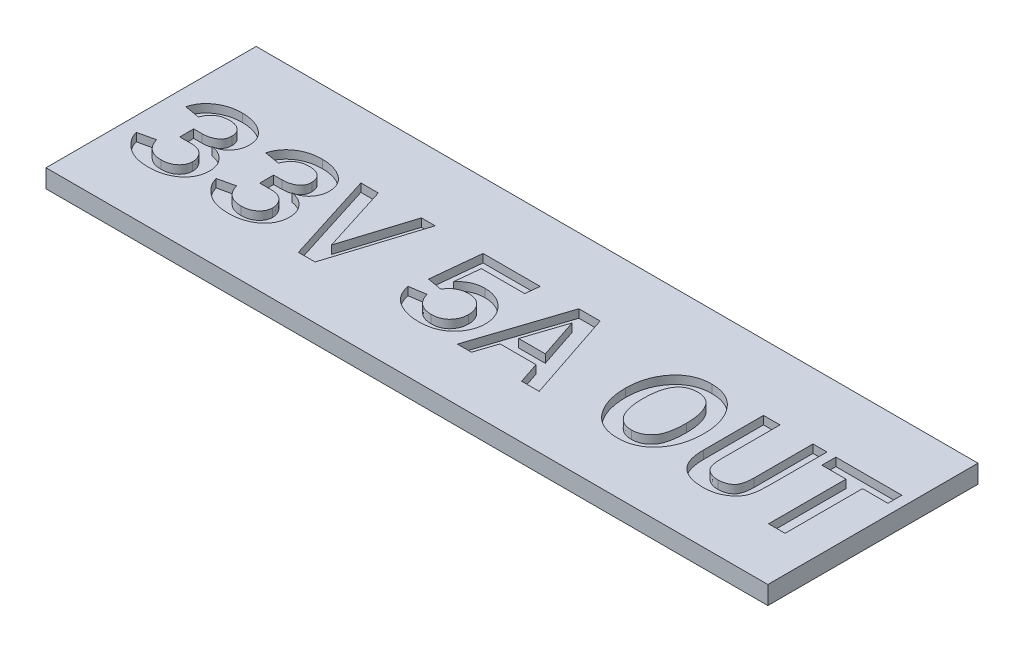
SolidWorks part; units mm, degrees
ref_plane "Front Plane" through (0, 0, 0) normal (0, 0, 1) x (1, 0, 0)
ref_plane "Top Plane" through (0, 0, 0) normal (0, 1, 0) x (1, 0, 0)
ref_plane "Right Plane" through (0, 0, 0) normal (1, 0, 0) x (0, 0, -1)
sketch "Sketch1" plane through (0, 0, 0) normal (0, 1, 0) x (1, 0, 0)
  line L1 (-13.5259, 12.0552) -> (25.9741, 12.0552)
  line L2 (-13.5259, 12.0552) -> (-13.5259, 0.5552)
  line L3 (-13.5259, 0.5552) -> (25.9741, 0.5552)
  line L4 (25.9741, 12.0552) -> (25.9741, 0.5552)
  dimension "D1" = 11.5
  dimension "D2" = 39.5
extrude "Boss-Extrude1" add sketch "Sketch1" along normal blind 1
sketch "Sketch2" plane through (0, 1, 0) normal (0, 1, 0) x (1, 0, 0)
  text T0 "33V 5A OUT" font "Franklin Gothic Medium" height 5
  point P1 (-12.0477, 2.2844)
  point P2 (-12.4693, 3.1599)
  point P3 (-13.0205, 3.1923)
  point P4 (-12.8908, 3.2247)
  point P5 (-12.9232, 3.4517)
extrude "Cut-Extrude1" cut sketch "Sketch2" against normal blind 0.45
